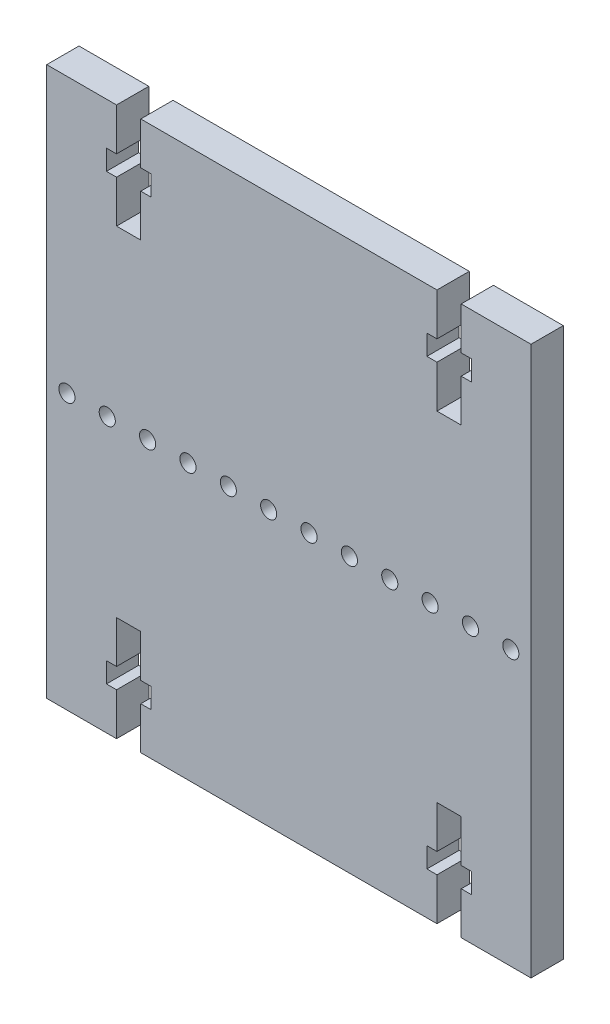
SolidWorks part; units mm, degrees
ref_plane "Спереди" through (0, 0, 0) normal (0, 0, 1) x (1, 0, 0)
ref_plane "Сверху" through (0, 0, 0) normal (0, 1, 0) x (1, 0, 0)
ref_plane "Справа" through (0, 0, 0) normal (1, 0, 0) x (0, 0, -1)
sketch "Эскиз2" plane through (0, 0, 0) normal (0, 0, 1) x (1, 0, 0)
  line L1 (0, 0) -> (60, 0)
  line L2 (0, 0) -> (0, 68)
  line L3 (0, 68) -> (60, 68)
  line L4 (60, 0) -> (60, 68)
  dimension "D1" = 68
  dimension "D2" = 60
extrude "Бобышка-Вытянуть1" add sketch "Эскиз2" along normal blind 4
sketch "Эскиз3" plane through (0, 0, 4) normal (0, 0, 1) x (1, 0, 0)
  line L0 (8.65, 0) -> (8.65, 5.25)
  line L1 (0, 0) -> (60, 0) construction
  line L2 (8.65, 5.25) -> (7.4, 5.25)
  line L3 (7.4, 5.25) -> (7.4, 7.75)
  line L4 (7.4, 7.75) -> (8.65, 7.75)
  line L5 (8.65, 7.75) -> (8.65, 13)
  line L6 (8.65, 13) -> (11.65, 13)
  line L7 (10.15, 13) -> (10.15, 0) construction
  line L8 (11.65, 0) -> (11.65, 5.25)
  line L9 (11.65, 5.25) -> (12.9, 5.25)
  line L10 (12.9, 5.25) -> (12.9, 7.75)
  line L11 (12.9, 7.75) -> (11.65, 7.75)
  line L12 (11.65, 7.75) -> (11.65, 13)
  line L13 (0, 68) -> (0, 0) construction
  line L14 (60, 0) -> (60, 68) construction
  line L16 (47.1, 7.75) -> (48.35, 7.75)
  line L17 (47.1, 5.25) -> (47.1, 7.75)
  line L18 (48.35, 5.25) -> (47.1, 5.25)
  line L19 (48.35, 0) -> (48.35, 5.25)
  line L20 (51.35, 0) -> (51.35, 5.25)
  line L21 (51.35, 5.25) -> (52.6, 5.25)
  line L22 (52.6, 5.25) -> (52.6, 7.75)
  line L23 (52.6, 7.75) -> (51.35, 7.75)
  line L24 (51.35, 7.75) -> (51.35, 13)
  line L25 (51.35, 13) -> (48.35, 13)
  line L26 (48.35, 7.75) -> (48.35, 13)
  line L27 (8.65, 0) -> (11.65, 0)
  line L28 (48.35, 0) -> (51.35, 0)
  line L29 (0, 34) -> (9.5, 34) construction
  line L30 (48.35, 68) -> (48.35, 62.75)
  line L31 (48.35, 62.75) -> (47.1, 62.75)
  line L32 (47.1, 62.75) -> (47.1, 60.25)
  line L33 (47.1, 60.25) -> (48.35, 60.25)
  line L34 (48.35, 60.25) -> (48.35, 55)
  line L35 (51.35, 55) -> (48.35, 55)
  line L36 (51.35, 60.25) -> (51.35, 55)
  line L37 (52.6, 60.25) -> (51.35, 60.25)
  line L38 (52.6, 62.75) -> (52.6, 60.25)
  line L39 (51.35, 62.75) -> (52.6, 62.75)
  line L40 (51.35, 68) -> (51.35, 62.75)
  line L41 (48.35, 68) -> (51.35, 68)
  line L42 (8.65, 68) -> (8.65, 62.75)
  line L43 (8.65, 62.75) -> (7.4, 62.75)
  line L44 (7.4, 62.75) -> (7.4, 60.25)
  line L45 (7.4, 60.25) -> (8.65, 60.25)
  line L46 (8.65, 60.25) -> (8.65, 55)
  line L47 (8.65, 55) -> (11.65, 55)
  line L48 (11.65, 60.25) -> (11.65, 55)
  line L49 (12.9, 60.25) -> (11.65, 60.25)
  line L50 (12.9, 62.75) -> (12.9, 60.25)
  line L51 (11.65, 62.75) -> (12.9, 62.75)
  line L52 (11.65, 68) -> (11.65, 62.75)
  line L53 (8.65, 68) -> (11.65, 68)
  dimension "D1" = 7.4
  dimension "D2" = 3
  dimension "D3" = 13
  dimension "D4" = 2.5
  dimension "D5" = 5.5
  dimension "D6" = 7.4
extrude "Вырез-Вытянуть1" cut sketch "Эскиз3" against normal blind 4
sketch "Эскиз4" plane through (0, 0, 4) normal (0, 0, 1) x (1, 0, 0)
  line L1 (0, 68) -> (0, 0) construction
  line L2 (60, 0) -> (60, 68) construction
  circle A0 centre (2.5, 34) radius 1
  circle A1 centre (7.5, 34) radius 1
  circle A2 centre (12.5, 34) radius 1
  circle A3 centre (17.5, 34) radius 1
  circle A4 centre (22.5, 34) radius 1
  circle A5 centre (27.5, 34) radius 1
  circle A6 centre (32.5, 34) radius 1
  circle A7 centre (37.5, 34) radius 1
  circle A8 centre (42.5, 34) radius 1
  circle A9 centre (47.5, 34) radius 1
  circle A10 centre (52.5, 34) radius 1
  circle A11 centre (57.5, 34) radius 1
  point P30 (60, 34)
  dimension "D1" = 2
  dimension "D3" = 2.5
  dimension "D5" = 2.5
  dimension "D4" = 12
extrude "Вырез-Вытянуть2" cut sketch "Эскиз4" against normal blind 4
